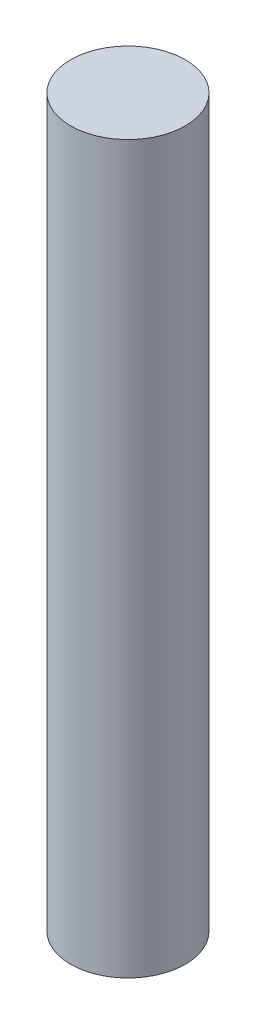
SolidWorks part; units mm, degrees
ref_plane "Front" through (0, 0, 0) normal (0, 0, 1) x (1, 0, 0)
ref_plane "Top" through (0, 0, 0) normal (0, 1, 0) x (1, 0, 0)
ref_plane "Right" through (0, 0, 0) normal (1, 0, 0) x (0, 0, -1)
sketch "Sketch1" plane through (0, 0, 0) normal (0, 1, 0) x (1, 0, 0)
  circle A0 centre (0, 0) radius 1.5
  dimension "D1" = 3
extrude "Boss-Extrude1" add sketch "Sketch1" along normal blind 19
